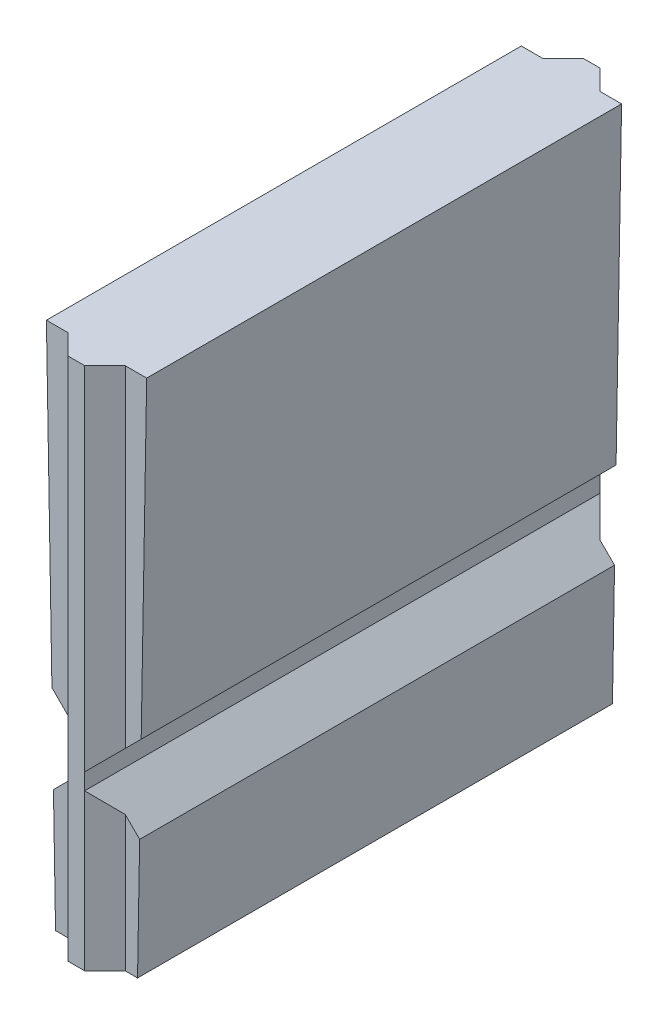
SolidWorks part; units mm, degrees
ref_plane "Front" through (0, 0, 0) normal (0, 0, 1) x (1, 0, 0)
ref_plane "Top" through (0, 0, 0) normal (0, 1, 0) x (1, 0, 0)
ref_plane "Right" through (0, 0, 0) normal (1, 0, 0) x (0, 0, -1)
sketch "Sketch1" plane through (0, 0, 0) normal (0, 0, 1) x (1, 0, 0)
  line L0 (-1.1421, 0) -> (1.1421, 0)
  line L1 (1.1421, 0) -> (1.397, 14.605)
  line L2 (1.397, 14.605) -> (-1.397, 14.605)
  line L3 (-1.397, 14.605) -> (-1.1421, 0)
  line L4 (0, 0) -> (0, 6.9537) construction
  dimension "D1" = 1.397
  dimension "D2" = 2.794
  dimension "D3" = 2
  dimension "D4" = 1
  dimension "D5" = 14.605
extrude "Boss-Extrude1" add sketch "Sketch1" along normal blind 13.2334
sketch "Sketch2" plane through (0, 0, 0) normal (0, -1, 0) x (1, 0, 0)
  line L0 (-0.8001, 13.2334) -> (0.8001, 13.2334)
  line L1 (-1.1421, 13.2334) -> (1.1421, 13.2334) construction
  line L2 (0.8001, 13.2334) -> (0.2311, 13.7973)
  line L3 (0.2311, 13.7973) -> (-0.2337, 13.7973)
  line L4 (-0.2337, 13.7973) -> (-0.8001, 13.2334)
  line L5 (0, 0) -> (0, 14.9357) construction
  dimension "D1" = 0.8001
  dimension "D2" = 1.6002
  dimension "D3" = 0.2311
  dimension "D4" = 0.4648
  dimension "D5" = 0.5639
  dimension "D6" = 90.386
extrude "Boss-Extrude2" add sketch "Sketch2" against normal up to surface (14.605 mm away) up to face at (0, 14.605, 6.6167)
ref_plane "Plane1" through (0, 0, 6.6167) normal (0, 0, 1) x (1, 0, 0)
mirror "Mirror1" about plane through (0, 0, 6.6167) normal (0, 0, 1) of "Boss-Extrude2"
sketch "Sketch3" plane through (0, 0, 13.7973) normal (0, 0, 1) x (1, 0, 0)
  line L0 (-1.2435, 5.813) -> (-0.2337, 4.8006)
  line L1 (-1.397, 14.605) -> (-1.1421, 0) construction
  line L2 (-0.2337, 14.605) -> (-0.2337, 0) construction
  line L3 (-0.2337, 4.8006) -> (-0.2337, 4.3434)
  line L4 (-0.2337, 4.3434) -> (-1.201, 3.3748)
  line L5 (-1.201, 3.3748) -> (-1.2435, 5.813)
  line L6 (1.2435, 5.813) -> (0.2311, 4.8006)
  line L7 (1.1421, 0) -> (1.397, 14.605) construction
  line L8 (0.2311, 14.605) -> (0.2311, 0) construction
  line L9 (0.2311, 4.8006) -> (0.2311, 4.3434)
  line L10 (0.2311, 4.3434) -> (1.201, 3.3748)
  line L11 (1.201, 3.3748) -> (1.2435, 5.813)
  line L12 (-0.8001, 14.605) -> (-1.397, 14.605) construction
  line L13 (-0.2337, 4.572) -> (2.4579, 4.572) construction
  dimension "D1" = 9.8044
  dimension "D2" = 0.4572
extrude "Cut-Extrude1" cut sketch "Sketch3" against normal up to surface (14.3612 mm away) up to face at (-0.0013, 7.3025, -0.5639)
